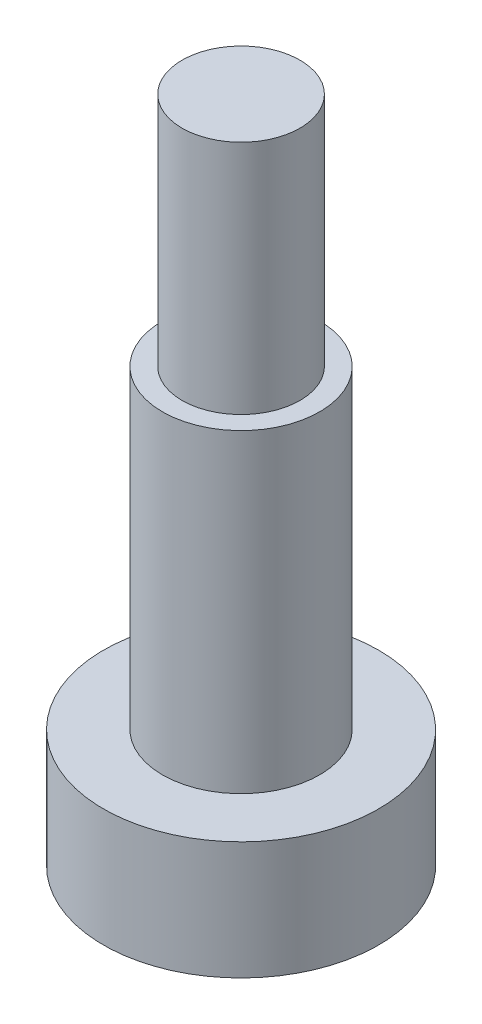
SolidWorks part; units mm, degrees
material "1060 合金"
ref_plane "前视基准面" through (0, 0, 0) normal (0, 0, 1) x (1, 0, 0)
ref_plane "上视基准面" through (0, 0, 0) normal (0, 1, 0) x (1, 0, 0)
ref_plane "右视基准面" through (0, 0, 0) normal (1, 0, 0) x (0, 0, -1)
sketch "草图1" plane through (0, 0, 0) normal (0, 1, 0) x (1, 0, 0)
  circle A0 centre (0, 0) radius 2
  dimension "D1" = 4
extrude "凸台-拉伸1" add sketch "草图1" along normal blind 8
sketch "草图2" plane through (0, 8, 0) normal (0, 1, 0) x (1, 0, 0)
  circle A0 centre (0, 0) radius 1.5
  dimension "D1" = 3
extrude "凸台-拉伸2" add sketch "草图2" along normal blind 6
cosmetic thread "装饰螺纹线1" parameters "D2"=2.459
sketch "草图3" plane through (0, 0, 0) normal (0, -1, 0) x (1, 0, 0)
  circle A0 centre (0, 0) radius 3.5
  dimension "D1" = 7
extrude "凸台-拉伸3" add sketch "草图3" along normal blind 3
